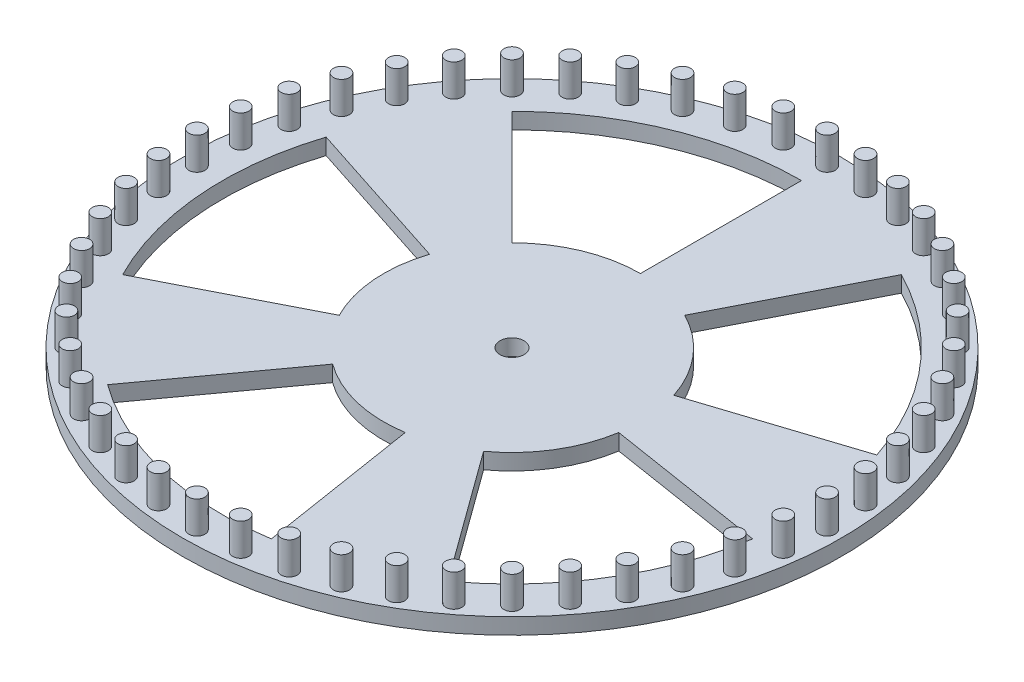
SolidWorks part; units mm, degrees
ref_plane "Front Plane" through (0, 0, 0) normal (0, 0, 1) x (1, 0, 0)
ref_plane "Top Plane" through (0, 0, 0) normal (0, 1, 0) x (1, 0, 0)
ref_plane "Right Plane" through (0, 0, 0) normal (1, 0, 0) x (0, 0, -1)
sketch "Sketch1" plane through (0, 0, 0) normal (0, 1, 0) x (1, 0, 0)
  circle A0 centre (19.4893, 73.6636) radius 130.175
  dimension "D1" = 260.35
extrude "Extrude1" add sketch "Sketch1" along normal blind 6.35
sketch "Sketch2" plane through (0, 6.35, 0) normal (0, 1, 0) x (-1, 0, 0)
  line L0 (-19.4893, -73.6636) -> (-170.8592, -73.6636) construction
  line L1 (-19.4893, -73.6636) -> (122.9773, -73.6636) construction
  line L2 (-19.4893, -73.6636) -> (-165.1915, -100.0896) construction
  line L3 (-19.4893, -73.6636) -> (-160.7402, -126.6438) construction
  line L4 (-19.4893, -73.6636) -> (-151.2289, -152.3208) construction
  circle A0 centre (-19.4893, -73.6636) radius 124.46 construction
  circle A1 centre (-143.9493, -73.6636) radius 3.175
  dimension "D1" = 248.92
  dimension "D2" = 6.35
sketch "Sketch3" plane through (0, 6.35, 0) normal (0, 1, 0) x (1, 0, 0)
  circle A0 centre (19.4893, 73.6636) radius 4.7625
  dimension "D1" = 9.525
extrude "Extrude3" cut sketch "Sketch3" against normal blind 6.35
extrude "Extrude4" add sketch "Sketch2" along normal blind 12.7
pattern_circular "CirPattern1" count 48 over 360 about axis through (19.4893, 0, -73.6636) along (0, 1, 0) of "Extrude4"
sketch "Sketch5" plane through (0, 6.35, 0) normal (0, 1, 0) x (1, 0, 0)
  line L0 (-16.382, 109.5349) -> (-61.3693, 154.5222)
  line L1 (19.4893, 124.3933) -> (19.4893, 188.015)
  arc A0 (19.4893, 188.015) -> (-61.3693, 154.5222) centre (19.4893, 73.6636) ccw
  arc A1 (19.4893, 124.3933) -> (-16.382, 109.5349) centre (19.4893, 73.6636) ccw
  point P3 (0, 0)
extrude "Extrude5" cut sketch "Sketch5" against normal blind 19.05
pattern_circular "CirPattern2" count 5 over 360 about axis through (19.4893, 0, -73.6636) along (0, 1, 0) of "Extrude5"
